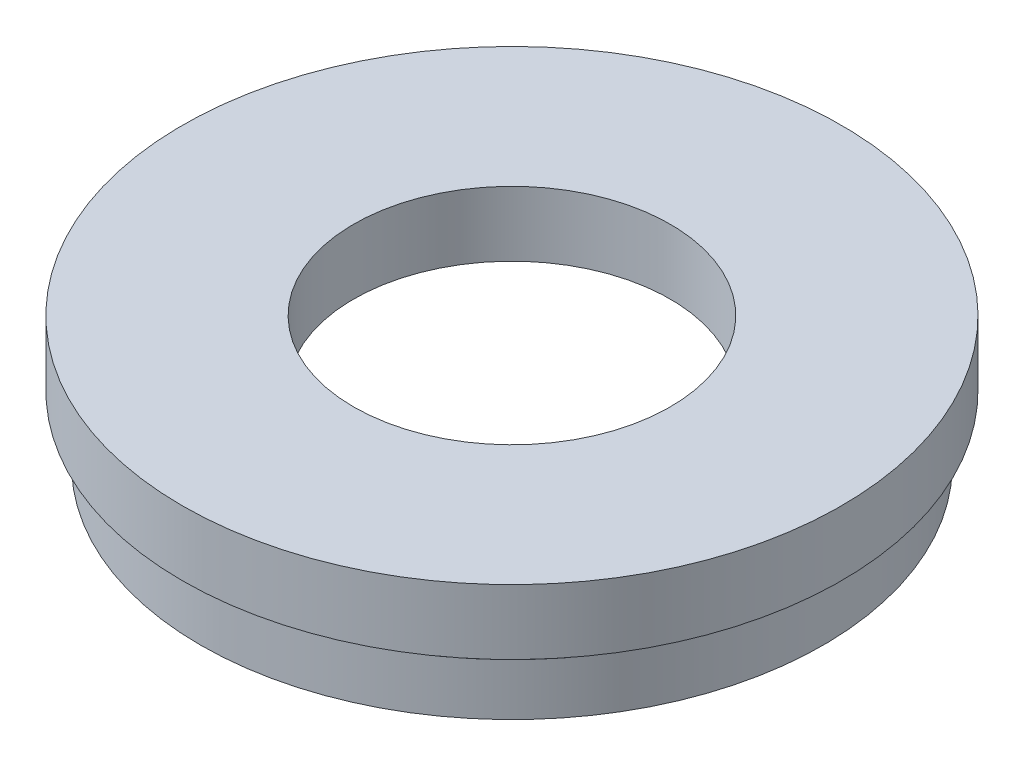
SolidWorks part; units mm, degrees
ref_plane "前视基准面" through (0, 0, 0) normal (0, 0, 1) x (1, 0, 0)
ref_plane "上视基准面" through (0, 0, 0) normal (0, 1, 0) x (1, 0, 0)
ref_plane "右视基准面" through (0, 0, 0) normal (1, 0, 0) x (0, 0, -1)
sketch "草图1" plane through (0, 0, 0) normal (0, 0, 1) x (1, 0, 0)
  line L0 (0, 17.4193) -> (0, -25.7883) construction
  line L1 (20.5, 0) -> (20.5, 4)
  line L2 (20.5, 4) -> (21.1, 4)
  line L3 (21.1, 4) -> (21.1, 5)
  line L4 (21.1, 5) -> (12.2, 5)
  line L5 (12.2, 5) -> (12.2, 10)
  line L6 (12.2, 10) -> (25.4, 10)
  line L7 (20.5, 0) -> (24, 0)
  line L8 (24, 0) -> (24, 4)
  line L9 (24, 4) -> (23.5, 4)
  line L10 (23.5, 4) -> (23.5, 5)
  line L11 (23.5, 5) -> (25.4, 5)
  line L12 (25.4, 5) -> (25.4, 10)
  dimension "D1" = 20.5
  dimension "D2" = 21.1
  dimension "D3" = 12.2
  dimension "D4" = 24
  dimension "D5" = 23.5
  dimension "D6" = 25.4
  dimension "D7" = 1
  dimension "D8" = 1
  dimension "D9" = 5
  dimension "D10" = 10
revolve "旋转1" add sketch "草图1" angle 360 about L0
cosmetic thread "装饰螺纹线1" parameters "D2"=25.4
cosmetic thread "装饰螺纹线2" parameters "D2"=42
cosmetic thread "装饰螺纹线3" parameters "D2"=47
